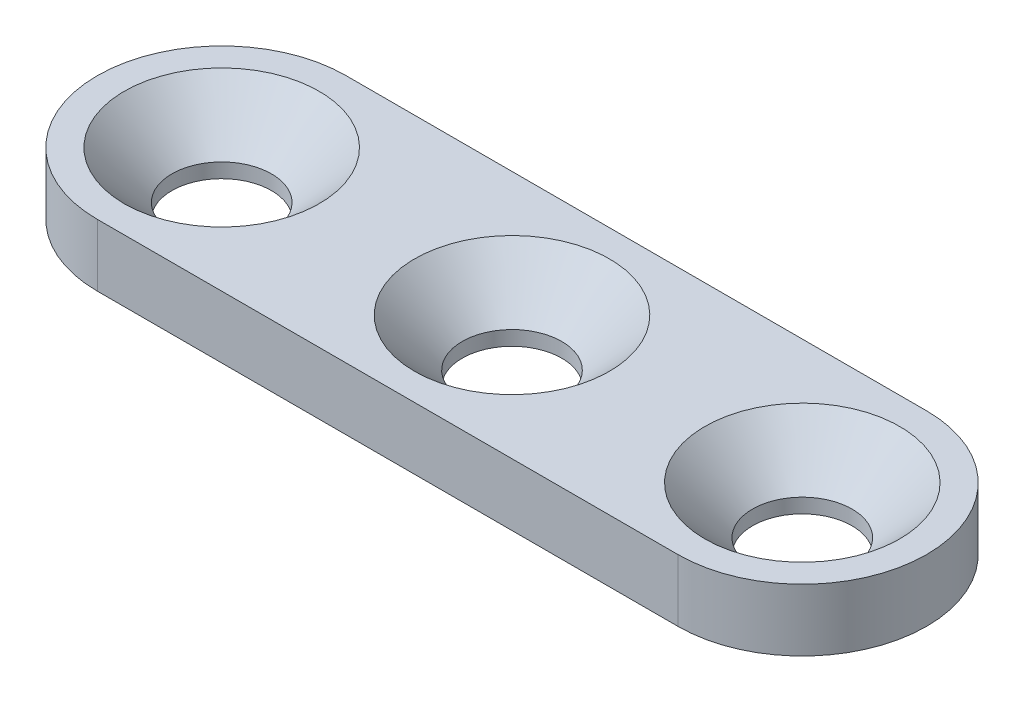
SolidWorks part; units mm, degrees
material "3003 Alloy"
ref_plane "Front Plane" through (0, 0, 0) normal (0, 0, 1) x (1, 0, 0)
ref_plane "Top Plane" through (0, 0, 0) normal (0, 1, 0) x (1, 0, 0)
ref_plane "Right Plane" through (0, 0, 0) normal (1, 0, 0) x (0, 0, -1)
sketch "Sketch1" plane through (0, 0, 0) normal (0, 1, 0) x (1, 0, 0)
  line L0 (-28, 0) -> (0, 0) construction
  line L3 (-28, 6) -> (0, 6)
  line L4 (-28, -6) -> (0, -6)
  line L5 (-14, 6) -> (-14, -6) construction
  arc A2 (-28, 6) -> (-28, -6) centre (-28, 0) ccw
  arc A3 (0, -6) -> (0, 6) centre (0, 0) ccw
  circle A4 centre (-28, 0) radius 2
  circle A5 centre (-14, 0) radius 2
  circle A6 centre (0, 0) radius 2
  point P2 (-14, 0)
  dimension "D1" = 6
  dimension "D2" = 28
  dimension "D3" = 4
  dimension "D4" = 4
extrude "Boss-Extrude2" add sketch "Sketch1" along normal blind 3
hole_wizard "CSK for M4 Flat Head Machine Screw1" positions "Sketch5" profile "Sketch4" countersink size "M4" standard "ANSI Metric"
sketch "Sketch5" plane through (0, 3, 0) normal (0, 1, 0) x (1, 0, 0)
  point P0 (-14, 0)
sketch "Sketch4" plane through (-14, 3, 0) normal (1, 0, 0) x (0, 0, 1)
  line L0 (0, 0) -> (0, 23.6721)
  line L1 (0, 23.6721) -> (2.4, 22.23)
  line L2 (2.4, 22.23) -> (2.4, 2.3)
  line L3 (2.4, 2.3) -> (4.7, 0)
  line L5 (4.7, 0) -> (0, 0)
  line L6 (-2.4, 2.3) -> (-4.7, 0) construction
  line L10 (0, 23.6721) -> (-2.4, 22.23) construction
  line L11 (0, -6.35) -> (0, 107.95) construction
  dimension "Hole Dia." = 4.8
  dimension "Hole Depth" = 22.23
  dimension "Near C'Sink Dia." = 9.4
  dimension "Near C'Sink Angle" = 90
  dimension "Drill Angle" = 118
hole_wizard "CSK for M4 Flat Head Machine Screw2" positions "Sketch8" profile "Sketch7" countersink size "M4" standard "ANSI Metric"
sketch "Sketch8" plane through (0, 3, 0) normal (0, 1, 0) x (1, 0, 0)
  point P0 (-28, 0)
  point P3 (0, 0)
sketch "Sketch7" plane through (-28, 3, 0) normal (1, 0, 0) x (0, 0, 1)
  line L0 (0, 0) -> (0, 23.6721)
  line L1 (0, 23.6721) -> (2.4, 22.23)
  line L2 (2.4, 22.23) -> (2.4, 2.3)
  line L3 (2.4, 2.3) -> (4.7, 0)
  line L5 (4.7, 0) -> (0, 0)
  line L6 (-2.4, 2.3) -> (-4.7, 0) construction
  line L10 (0, 23.6721) -> (-2.4, 22.23) construction
  line L11 (0, -6.35) -> (0, 107.95) construction
  dimension "Hole Dia." = 4.8
  dimension "Hole Depth" = 22.23
  dimension "Near C'Sink Dia." = 9.4
  dimension "Near C'Sink Angle" = 90
  dimension "Drill Angle" = 118
